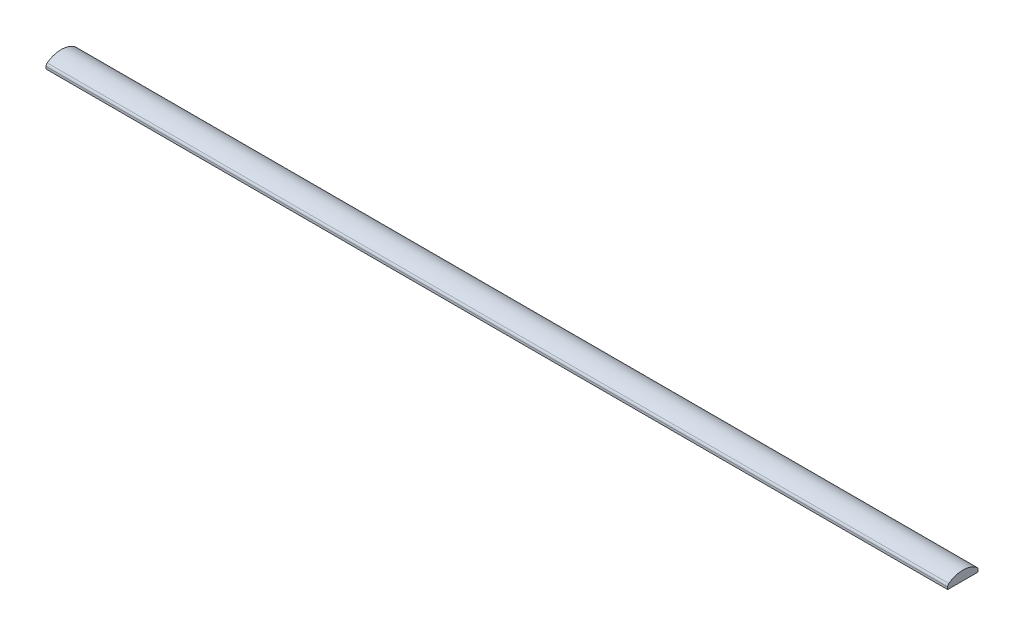
SolidWorks part; units mm, degrees
ref_plane "Front Plane" through (0, 0, 0) normal (0, 0, 1) x (1, 0, 0)
ref_plane "Top Plane" through (0, 0, 0) normal (0, 1, 0) x (1, 0, 0)
ref_plane "Right Plane" through (0, 0, 0) normal (1, 0, 0) x (0, 0, -1)
sketch "Sketch1" plane through (0, 0, 0) normal (1, 0, 0) x (0, 0, -1)
  line L0 (0, 2.475) -> (0, -0.625) construction
  line L1 (-5.05, -0.625) -> (5.05, -0.625)
  line L2 (-5.05, -0.625) -> (-5.05, 0.1417)
  line L3 (-5.05, 0.625) -> (5.05, 0.625) construction
  line L4 (5.05, -0.625) -> (5.05, 0.1417)
  line L5 (-5.05, -0.625) -> (5.05, 0.625) construction
  line L6 (-5.05, 0.625) -> (5.05, -0.625) construction
  arc A0 (-4.6441, 0.9461) -> (4.6441, 0.9461) centre (0, -5.3426) cw
  arc A1 (5.05, 0.1417) -> (4.6441, 0.9461) centre (4.05, 0.1417) ccw
  arc A2 (-5.05, 0.1417) -> (-4.6441, 0.9461) centre (-4.05, 0.1417) cw
  point P0 (0, 0)
  dimension "D3" = 3.1
  dimension "D4" = 1
  dimension "D1" = 1.25
  dimension "D2" = 10.1
extrude "Boss-Extrude1" add sketch "Sketch1" along normal mid plane 300
